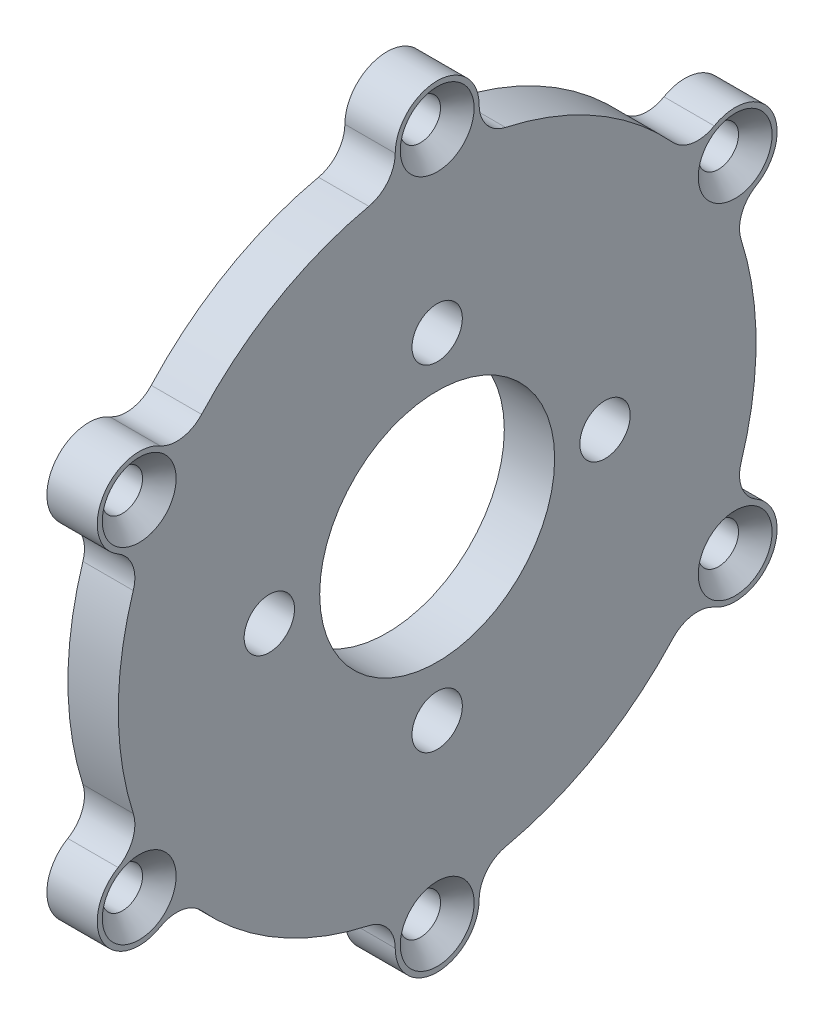
SolidWorks part; units mm, degrees
material "A-Glass Fiber"
ref_plane "Front Plane" through (0, 0, 0) normal (0, 0, 1) x (1, 0, 0)
ref_plane "Top Plane" through (0, 0, 0) normal (0, 1, 0) x (1, 0, 0)
ref_plane "Right Plane" through (0, 0, 0) normal (1, 0, 0) x (0, 0, -1)
sketch "Sketch1" plane through (0, 0, 0) normal (0, 0, 1) x (1, 0, 0)
  line L0 (0, 0) -> (-13.0355, 0) construction
  line L1 (1.5, 7) -> (-1.5, 7)
  line L2 (1.5, 7) -> (1.5, 19)
  line L3 (1.5, 19) -> (-1.5, 19)
  line L4 (-1.5, 7) -> (-1.5, 19)
  line L5 (1.5, 7) -> (-1.5, 19) construction
  line L6 (1.5, 19) -> (-1.5, 7) construction
  point P0 (0, 13)
  dimension "D1" = 3
  dimension "D2" = 14
  dimension "D3" = 38
revolve "Revolve1" add sketch "Sketch1" angle 360 about L0
hole_wizard "Ø3.0 (3) Diameter Hole2" positions "Sketch5" profile "Sketch4" hole size "Ø3.0" standard "DIN"
sketch "Sketch5" plane through (1.5, 0, 0) normal (1, 0, 0) x (0, 0, -1)
  circle A0 centre (0, 0) radius 10
  point P0 (0, 10)
  dimension "D1" = 20
sketch "Sketch4" plane through (1.5, 10, 0) normal (0, 1, 0) x (0, 0, -1)
  line L0 (0, 0) -> (0, 6.9013)
  line L1 (0, 6.9013) -> (1.5, 6)
  line L2 (1.5, 6) -> (1.5, 0)
  line L5 (1.5, 0) -> (0, 0)
  line L10 (0, 6.9013) -> (-1.5, 6) construction
  line L11 (0, -6.35) -> (0, 107.95) construction
  dimension "Hole Dia." = 3
  dimension "Hole Depth" = 6
  dimension "Drill Angle" = 118
pattern_circular "CirPattern1" count 4 over 360 about axis through (0, 0, 0) along (1, 0, 0) of "Ø3.0 (3) Diameter Hole2"
sketch "Sketch7" plane through (1.5, 0, 0) normal (1, 0, 0) x (0, 0, -1)
  circle A0 centre (0, 20.5) radius 2.5
  circle A1 centre (0, 0) radius 20.5 construction
  dimension "D1" = 5
  dimension "D2" = 41
extrude "Boss-Extrude1" add sketch "Sketch7" against normal up to surface (3 mm away) up to face at (-1.5, 0, -8.5)
sketch "Sketch8" plane through (1.5, 0, 0) normal (1, 0, 0) x (0, 0, -1)
  line L1 (2.5, 15.7129) -> (-2.5, 15.7129)
  line L2 (2.5, 15.7129) -> (2.5, 20.5)
  line L3 (2.5, 20.5) -> (-2.5, 20.5)
  line L4 (-2.5, 15.7129) -> (-2.5, 20.5)
  line L5 (2.5, 15.7129) -> (-2.5, 20.5) construction
  line L6 (2.5, 20.5) -> (-2.5, 15.7129) construction
  arc A0 (1.923, 18.9024) -> (-1.923, 18.9024) centre (0, 20.5) ccw construction
  point P0 (0, 18.1065)
extrude "Boss-Extrude2" add sketch "Sketch8" against normal up to surface (3 mm away)
hole_wizard "CSK for M2 Countersunk Flat Head Screw1" positions "Sketch10" profile "Sketch9" countersink size "M2" standard "DIN" end condition through all
sketch "Sketch10" plane through (1.5, 0, 0) normal (1, 0, 0) x (0, 0, -1)
  point P0 (0, 20.5)
sketch "Sketch9" plane through (1.5, 20.5, 0) normal (0, 1, 0) x (0, 0, -1)
  line L0 (0, 0) -> (0, 3)
  line L1 (0, 3) -> (1.2, 3)
  line L2 (1.2, 3) -> (1.2, 1)
  line L3 (1.2, 1) -> (2.2, 0)
  line L5 (2.2, 0) -> (0, 0)
  line L6 (-1.2, 1) -> (-2.2, 0) construction
  line L11 (0, -6.35) -> (0, 107.95) construction
  dimension "Thru Hole Dia." = 2.4
  dimension "Thru Hole Depth" = 3
  dimension "Near C'Sink Dia." = 4.4
  dimension "Near C'Sink Angle" = 90
pattern_circular "CirPattern2" count 6 over 360 about axis through (0, 0, 0) along (1, 0, 0) of "Boss-Extrude2", "Boss-Extrude1", "CSK for M2 Countersunk Flat Head Screw1"
fillet "Fillet1" radius 2 12 edges at (0, 11.5825, -15.0614) (0, 7.2523, -17.5614) (0, -7.2523, -17.5614) (0, -11.5825, -15.0614) (0, -18.8348, -2.5) (0, -18.8348, 2.5) (0, -11.5825, 15.0614) (0, -7.2523, 17.5614) (0, 7.2523, 17.5614) (0, 11.5825, 15.0614) (0, 18.8348, -2.5) (0, 18.8348, 2.5)
sketch "Sketch12" plane through (-1.5, 0, 0) normal (-1, 0, 0) x (0, 0, 1)
  circle A0 centre (0, 0) radius 17
  circle A1 centre (0, 0) radius 12.5
  dimension "D1" = 4.5
  dimension "D2" = 25
extrude "Cut-Extrude1" cut sketch "Sketch12" against normal blind 1.5
fillet "Fillet2" radius 0.5 2 edges at (0, 0, 17) (0, 0, 12.5)
